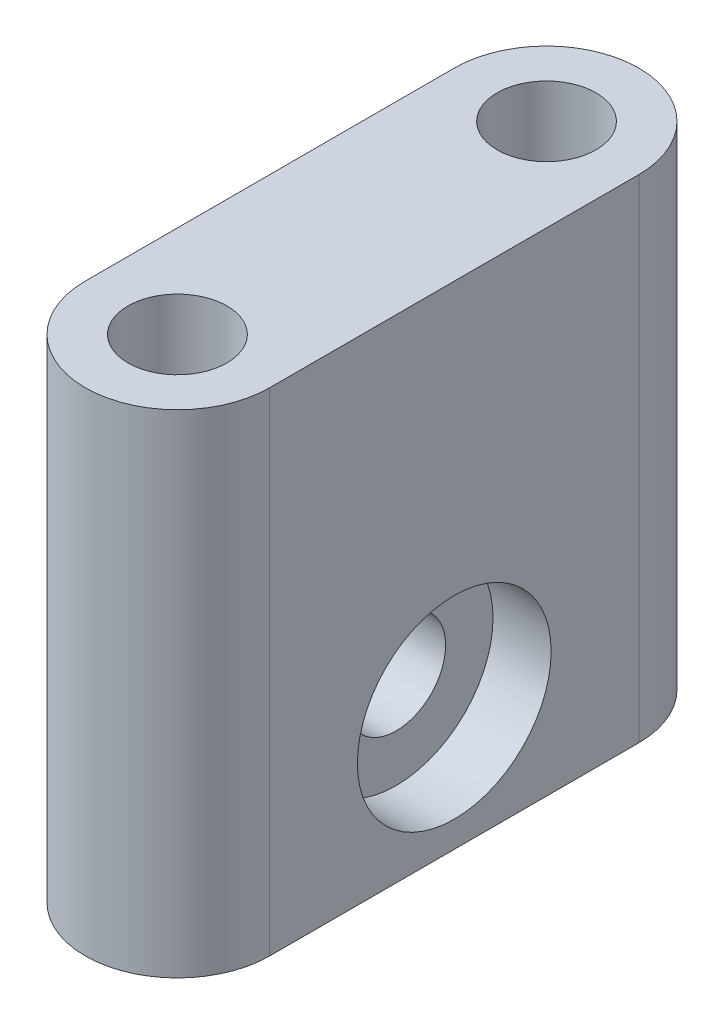
SolidWorks part; units mm, degrees
material "6061-T6 (SS)"
ref_plane "Front Plane" through (0, 0, 0) normal (0, 0, 1) x (1, 0, 0)
ref_plane "Top Plane" through (0, 0, 0) normal (0, 1, 0) x (1, 0, 0)
ref_plane "Right Plane" through (0, 0, 0) normal (1, 0, 0) x (0, 0, -1)
sketch "Sketch8" plane through (0, 0, 0) normal (0, 1, 0) x (1, 0, 0)
  line L0 (0, 19.05) -> (0, -19.05) construction
  line L1 (-31.75, -19.05) -> (31.75, -19.05)
  line L2 (-31.75, -19.05) -> (-31.75, 19.05)
  line L3 (-31.75, 19.05) -> (31.75, 19.05)
  line L4 (31.75, -19.05) -> (31.75, 19.05)
  line L5 (-31.75, -19.05) -> (31.75, 19.05) construction
  line L6 (-31.75, 19.05) -> (31.75, -19.05) construction
  line L7 (-15.875, 19.05) -> (-15.875, -19.05)
  point P0 (0, 0)
  dimension "D1" = 63.5
  dimension "D2" = 38.1
  dimension "D3" = 15.875
extrude "Boss-Extrude2" add sketch "Sketch8" along normal blind 25.4 contours L7 L3 L2 L1
sketch "Sketch9" plane through (0, 0, 0) normal (0, 1, 0) x (1, 0, 0)
  line L1 (31.75, 19.05) -> (-15.875, 19.05) construction
  line L2 (31.75, 19.05) -> (31.75, -19.05) construction
  line L3 (31.75, -19.05) -> (-15.875, -19.05) construction
  line L4 (-15.875, 19.05) -> (-15.875, -19.05) construction
  line L6 (7.9375, 19.05) -> (7.9375, 0) construction
  line L7 (-15.875, 0) -> (7.9375, 0) construction
  line L8 (-15.875, 0) -> (7.9375, 19.05) construction
  line L9 (-15.875, 19.05) -> (7.9375, 0) construction
  line L10 (-31.75, 19.05) -> (-15.875, 0) construction
  line L11 (-15.875, 19.05) -> (-31.75, 0) construction
  line L12 (-15.875, 19.05) -> (-15.875, -19.05) construction
  point P10 (-3.9688, 9.525)
  point P14 (19.8438, 9.525)
  point P15 (19.8438, 0)
  point P16 (-3.9688, -9.525)
  point P17 (19.8438, -9.525)
  point P18 (-3.9688, 0)
  point P20 (-23.8125, 9.525)
  point P24 (-23.8125, -9.525)
sketch "Sketch10" plane through (0, 0, 0) normal (0, 1, 0) x (1, 0, 0)
  line L0 (-31.75, 0) -> (-15.875, 0) construction
  line L1 (-28.575, 9.525) -> (-28.575, -9.525)
  line L2 (-19.05, 9.525) -> (-19.05, -9.525)
  line L4 (-31.75, 19.05) -> (-15.875, 19.05)
  line L5 (-31.75, 19.05) -> (-31.75, -19.05)
  line L6 (-31.75, -19.05) -> (-15.875, -19.05)
  line L7 (-15.875, 19.05) -> (-15.875, -19.05)
  arc A0 (-28.575, 9.525) -> (-19.05, 9.525) centre (-23.8125, 9.525) cw
  arc A1 (-28.575, -9.525) -> (-19.05, -9.525) centre (-23.8125, -9.525) ccw
  point P9 (-28.575, 0)
  point P13 (-19.05, 0)
  dimension "D1" = 9.525
hole_wizard "1/4-20 Tapped Hole1" positions "Sketch11" profile "Sketch12" tap size "1/4-20" standard "ANSI Inch"
sketch "Sketch11" plane through (0, 25.4, 0) normal (0, 1, 0) x (1, 0, 0)
  point P0 (-23.8125, 9.525)
  point P3 (-23.8125, -9.525)
sketch "Sketch12" plane through (-23.8125, 25.4, -9.525) normal (1, 0, 0) x (0, 0, 1)
  line L0 (0, 0) -> (0, 18.0438)
  line L1 (0, 18.0438) -> (2.5527, 16.51)
  line L2 (2.5527, 16.51) -> (2.5527, 0)
  line L5 (2.5527, 0) -> (0, 0)
  line L10 (0, 18.0438) -> (-2.5527, 16.51) construction
  line L11 (0, -6.35) -> (0, 107.95) construction
  dimension "Tap Drill Dia." = 5.1054
  dimension "Tap Drill Depth" = 16.51
  dimension "Drill Angle" = 118
cosmetic thread "Hole Thread1" parameters "D1"=12.7, "D2"=6.35
cosmetic thread "Hole Thread2" parameters "D1"=12.7, "D2"=6.35
extrude "Cut-Extrude2" cut sketch "Sketch10" along normal through all contours L5 L0 L1 A0 L2 L7 L4 | L0 L5 L6 L7 L2 A1 L1
sketch "Sketch13" plane through (0, 0, 0) normal (1, 0, 0) x (0, 0, -1)
  line L0 (0, 0) -> (0, 25.4) construction
  line L1 (9.525, 0) -> (-9.525, 0)
  line L2 (9.525, 0) -> (9.525, 25.4)
  line L3 (9.525, 25.4) -> (-9.525, 25.4)
  line L4 (-9.525, 0) -> (-9.525, 25.4)
  line L5 (0, 12.7) -> (-9.525, 0) construction
  circle A0 centre (0, 6.35) radius 3.175
  circle A1 centre (0, 6.35) radius 5
  point P9 (0, 12.7)
  point P10 (-4.7625, 6.35)
  point P12 (0, 6.35)
  dimension "D1" = 6.35
  dimension "D2" = 10
extrude "Cut-Extrude5" cut sketch "Sketch13" against normal blind 3 from surface at -19.05 contours A1 A0 | A0 starting at face at (-19.05, 12.7, 0)
hole_wizard "1/4-20 Tapped Hole2" positions "Sketch14" profile "Sketch15" tap size "1/4-20" standard "ANSI Inch"
sketch "Sketch14" plane through (-19.05, 0, 0) normal (1, 0, 0) x (0, 0, -1)
  point P0 (0, 6.35)
sketch "Sketch15" plane through (-19.05, 6.35, 0) normal (0, 1, 0) x (0, 0, -1)
  line L0 (0, 0) -> (0, 18.0438)
  line L1 (0, 18.0438) -> (2.5527, 16.51)
  line L2 (2.5527, 16.51) -> (2.5527, 0)
  line L5 (2.5527, 0) -> (0, 0)
  line L10 (0, 18.0438) -> (-2.5527, 16.51) construction
  line L11 (0, -6.35) -> (0, 107.95) construction
  dimension "Tap Drill Dia." = 5.1054
  dimension "Tap Drill Depth" = 16.51
  dimension "Drill Angle" = 118
cosmetic thread "Hole Thread3" parameters "D1"=12.7, "D2"=6.35
equation "\"D1@Sketch13\"=1/4in"
equation "\"D2@Sketch13\"=10mm"
